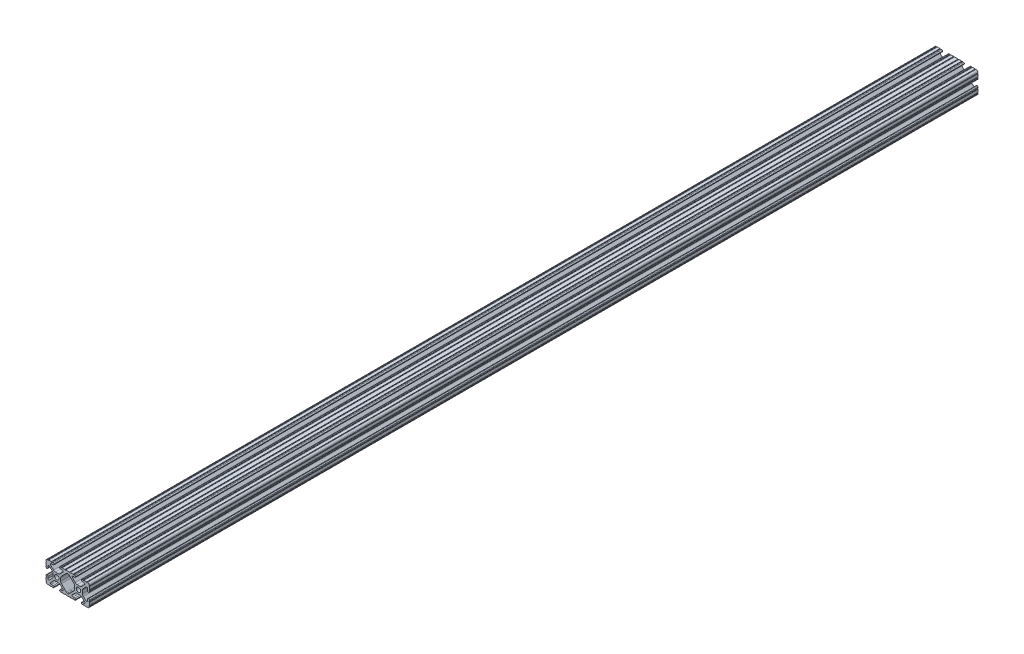
SolidWorks part; units mm, degrees
ref_plane "Front Plane" through (0, 0, 0) normal (0, 0, 1) x (1, 0, 0)
ref_plane "Top Plane" through (0, 0, 0) normal (0, 1, 0) x (1, 0, 0)
ref_plane "Right Plane" through (0, 0, 0) normal (1, 0, 0) x (0, 0, -1)
sketch "Sketch1" plane through (0, 0, 0) normal (0, 0, 1) x (1, 0, 0)
  line L0 (-7.2595, -3.8694) -> (-1.5457, -9.5728)
  line L1 (-8.1915, 1.6223) -> (-8.1915, -1.6223)
  line L2 (-1.504, 9.5765) -> (-7.252, 3.8768)
  line L3 (0.5515, 10.033) -> (-0.3952, 10.033)
  line L4 (7.2829, 3.8459) -> (1.6756, 9.5611)
  line L5 (8.1915, -1.6223) -> (8.1915, 1.6223)
  line L6 (1.5457, -9.5728) -> (7.2595, -3.8694)
  line L7 (-0.4332, -10.033) -> (0.4332, -10.033)
  line L8 (18.0171, 12.7) -> (16.9875, 12.7)
  line L9 (15.9385, 11.651) -> (15.9385, 11.5392)
  line L10 (16.9875, 10.4902) -> (19.1164, 10.4902)
  line L11 (19.8441, 8.7652) -> (16.619, 5.4551)
  line L12 (14.3449, 4.4958) -> (11.0833, 4.4958)
  line L13 (8.817, 5.4472) -> (5.5642, 8.7627)
  line L14 (6.2894, 10.4902) -> (8.4125, 10.4902)
  line L15 (9.4615, 11.5392) -> (9.4615, 11.651)
  line L16 (8.4125, 12.7) -> (7.3829, 12.7)
  line L17 (6.3669, 12.7) -> (3.1496, 12.7)
  line L18 (2.1336, 12.7) -> (-2.1336, 12.7)
  line L19 (-3.1496, 12.7) -> (-6.3669, 12.7)
  line L20 (-7.3829, 12.7) -> (-8.4125, 12.7)
  line L21 (-9.4615, 11.651) -> (-9.4615, 11.5392)
  line L22 (-8.4125, 10.4902) -> (-6.2836, 10.4902)
  line L23 (-5.5326, 8.6661) -> (-8.81, 5.4163)
  line L24 (-11.0455, 4.4958) -> (-14.3545, 4.4958)
  line L25 (-16.59, 5.4163) -> (-19.8674, 8.6661)
  line L26 (-19.1164, 10.4902) -> (-16.9875, 10.4902)
  line L27 (-15.9385, 11.5392) -> (-15.9385, 11.651)
  line L28 (-16.9875, 12.7) -> (-18.0171, 12.7)
  line L29 (-19.0331, 12.7) -> (-22.2504, 12.7)
  line L30 (-25.4, 9.5504) -> (-25.4, 6.3331)
  line L31 (-25.4, 5.3171) -> (-25.4, 4.2375)
  line L32 (-24.401, 3.2385) -> (-24.2392, 3.2385)
  line L33 (-23.1902, 4.2875) -> (-23.1902, 6.3347)
  line L34 (-21.434, 7.0665) -> (-18.148, 3.8082)
  line L35 (-17.2085, 1.5536) -> (-17.2085, -1.6952)
  line L36 (-18.1405, -3.9423) -> (-21.4316, -7.2274)
  line L37 (-23.1902, -6.498) -> (-23.1902, -4.2875)
  line L38 (-24.2392, -3.2385) -> (-24.351, -3.2385)
  line L39 (-25.4, -4.2875) -> (-25.4, -5.3171)
  line L40 (-25.4, -6.3331) -> (-25.4, -9.5504)
  line L41 (-22.2504, -12.7) -> (-19.0331, -12.7)
  line L42 (-18.0171, -12.7) -> (-16.9875, -12.7)
  line L43 (-15.9384, -11.651) -> (-15.9384, -11.5392)
  line L44 (-16.9875, -10.4902) -> (-19.1164, -10.4902)
  line L45 (-19.8341, -8.7551) -> (-16.4966, -5.4237)
  line L46 (-14.2536, -4.4958) -> (-11.1464, -4.4958)
  line L47 (-8.9034, -5.4237) -> (-5.5659, -8.7551)
  line L48 (-6.2836, -10.4902) -> (-8.4125, -10.4902)
  line L49 (-9.4616, -11.5392) -> (-9.4616, -11.651)
  line L50 (-8.4125, -12.7) -> (-7.3829, -12.7)
  line L51 (-6.3669, -12.7) -> (-3.1496, -12.7)
  line L52 (-2.1336, -12.7) -> (2.1336, -12.7)
  line L53 (3.1496, -12.7) -> (6.3669, -12.7)
  line L54 (7.3829, -12.7) -> (8.4125, -12.7)
  line L55 (9.4616, -11.651) -> (9.4616, -11.5392)
  line L56 (8.4125, -10.4902) -> (6.2894, -10.4902)
  line L57 (5.4807, -8.5353) -> (8.5979, -5.4237)
  line L58 (10.8409, -4.4958) -> (14.1026, -4.4958)
  line L59 (16.1879, -5.2766) -> (19.8682, -8.4822)
  line L60 (19.1164, -10.4902) -> (16.9875, -10.4902)
  line L61 (15.9384, -11.5392) -> (15.9384, -11.651)
  line L62 (16.9875, -12.7) -> (18.0171, -12.7)
  line L63 (19.0331, -12.7) -> (22.2504, -12.7)
  line L64 (25.4, -9.5504) -> (25.4, -6.3331)
  line L65 (25.4, -5.3171) -> (25.4, -4.2375)
  line L66 (24.401, -3.2385) -> (24.1892, -3.2385)
  line L67 (23.1902, -4.2375) -> (23.1902, -6.1559)
  line L68 (21.584, -6.8869) -> (18.2982, -4.025)
  line L69 (17.2085, -1.6308) -> (17.2085, 1.6308)
  line L70 (18.1094, 3.8465) -> (21.5263, 7.3534)
  line L71 (23.1902, 6.6769) -> (23.1902, 4.2375)
  line L72 (24.1892, 3.2385) -> (24.401, 3.2385)
  line L73 (25.4, 4.2375) -> (25.4, 5.3171)
  line L74 (25.4, 6.3332) -> (25.4, 9.5504)
  line L75 (22.2504, 12.7) -> (19.0331, 12.7)
  circle A0 centre (-12.7, 0) radius 2.6035
  circle A1 centre (12.7, 0) radius 2.6035
  arc A2 (-1.5457, -9.5728) -> (-0.4332, -10.033) centre (-0.4332, -8.4582) ccw
  arc A3 (-8.1915, -1.6223) -> (-7.2595, -3.8694) centre (-5.0165, -1.6223) ccw
  arc A4 (-7.252, 3.8768) -> (-8.1915, 1.6223) centre (-5.0165, 1.6223) ccw
  arc A5 (-0.3952, 10.033) -> (-1.504, 9.5765) centre (-0.3952, 8.4582) ccw
  arc A6 (1.6756, 9.5611) -> (0.5515, 10.033) centre (0.5515, 8.4582) ccw
  arc A7 (8.1915, 1.6223) -> (7.2829, 3.8459) centre (5.0165, 1.6223) ccw
  arc A8 (7.2595, -3.8694) -> (8.1915, -1.6223) centre (5.0165, -1.6223) ccw
  arc A9 (0.4332, -10.033) -> (1.5457, -9.5728) centre (0.4332, -8.4582) ccw
  arc A10 (18.0171, 12.7) -> (19.0331, 12.7) centre (18.5251, 12.7) ccw
  arc A11 (16.9875, 12.7) -> (15.9385, 11.651) centre (16.9875, 11.651) ccw
  arc A12 (15.9385, 11.5392) -> (16.9875, 10.4902) centre (16.9875, 11.5392) ccw
  arc A13 (19.8441, 8.7652) -> (19.1164, 10.4902) centre (19.1164, 9.4742) ccw
  arc A14 (14.3449, 4.4958) -> (16.619, 5.4551) centre (14.3449, 7.6708) ccw
  arc A15 (8.817, 5.4472) -> (11.0833, 4.4958) centre (11.0833, 7.6708) ccw
  arc A16 (6.2894, 10.4902) -> (5.5642, 8.7627) centre (6.2894, 9.4742) ccw
  arc A17 (8.4125, 10.4902) -> (9.4615, 11.5392) centre (8.4125, 11.5392) ccw
  arc A18 (9.4615, 11.651) -> (8.4125, 12.7) centre (8.4125, 11.651) ccw
  arc A19 (6.3669, 12.7) -> (7.3829, 12.7) centre (6.8749, 12.7) ccw
  arc A20 (2.1336, 12.7) -> (3.1496, 12.7) centre (2.6416, 12.7) ccw
  arc A21 (-3.1496, 12.7) -> (-2.1336, 12.7) centre (-2.6416, 12.7) ccw
  arc A22 (-7.3829, 12.7) -> (-6.3669, 12.7) centre (-6.8749, 12.7) ccw
  arc A23 (-8.4125, 12.7) -> (-9.4615, 11.651) centre (-8.4125, 11.651) ccw
  arc A24 (-9.4615, 11.5392) -> (-8.4125, 10.4902) centre (-8.4125, 11.5392) ccw
  arc A25 (-5.5326, 8.6661) -> (-6.2836, 10.4902) centre (-6.2836, 9.4235) ccw
  arc A26 (-11.0455, 4.4958) -> (-8.81, 5.4163) centre (-11.0455, 7.6708) ccw
  arc A27 (-16.59, 5.4163) -> (-14.3545, 4.4958) centre (-14.3545, 7.6708) ccw
  arc A28 (-19.1164, 10.4902) -> (-19.8674, 8.6661) centre (-19.1164, 9.4235) ccw
  arc A29 (-16.9875, 10.4902) -> (-15.9385, 11.5392) centre (-16.9875, 11.5392) ccw
  arc A30 (-15.9385, 11.651) -> (-16.9875, 12.7) centre (-16.9875, 11.651) ccw
  arc A31 (-19.0331, 12.7) -> (-18.0171, 12.7) centre (-18.5251, 12.7) ccw
  arc A32 (-23.2664, 12.6998) -> (-22.2504, 12.7) centre (-22.7584, 12.7) ccw
  arc A33 (-23.2664, 12.6998) -> (-25.3998, 10.5664) centre (-23.2918, 10.5918) ccw
  arc A34 (-25.4, 9.5504) -> (-25.3998, 10.5664) centre (-25.4, 10.0584) ccw
  arc A35 (-25.4, 5.3171) -> (-25.4, 6.3331) centre (-25.4, 5.8251) ccw
  arc A36 (-25.4, 4.2375) -> (-24.401, 3.2385) centre (-24.401, 4.2375) ccw
  arc A37 (-24.2392, 3.2385) -> (-23.1902, 4.2875) centre (-24.2392, 4.2875) ccw
  arc A38 (-21.434, 7.0665) -> (-23.1902, 6.3347) centre (-22.1596, 6.3347) ccw
  arc A39 (-17.2085, 1.5536) -> (-18.148, 3.8082) centre (-20.3835, 1.5536) ccw
  arc A40 (-18.1405, -3.9423) -> (-17.2085, -1.6952) centre (-20.3835, -1.6952) ccw
  arc A41 (-23.1902, -6.498) -> (-21.4316, -7.2274) centre (-22.1596, -6.498) ccw
  arc A42 (-23.1902, -4.2875) -> (-24.2392, -3.2385) centre (-24.2392, -4.2875) ccw
  arc A43 (-24.351, -3.2385) -> (-25.4, -4.2875) centre (-24.351, -4.2875) ccw
  arc A44 (-25.4, -6.3331) -> (-25.4, -5.3171) centre (-25.4, -5.8251) ccw
  arc A45 (-25.3998, -10.5664) -> (-25.4, -9.5504) centre (-25.4, -10.0584) ccw
  arc A46 (-25.3998, -10.5664) -> (-23.2664, -12.6998) centre (-23.2918, -10.5918) ccw
  arc A47 (-22.2504, -12.7) -> (-23.2664, -12.6998) centre (-22.7584, -12.7) ccw
  arc A48 (-18.0171, -12.7) -> (-19.0331, -12.7) centre (-18.5251, -12.7) ccw
  arc A49 (-16.9875, -12.7) -> (-15.9384, -11.651) centre (-16.9875, -11.651) ccw
  arc A50 (-15.9384, -11.5392) -> (-16.9875, -10.4902) centre (-16.9875, -11.5392) ccw
  arc A51 (-19.8341, -8.7551) -> (-19.1164, -10.4902) centre (-19.1164, -9.4742) ccw
  arc A52 (-14.2536, -4.4958) -> (-16.4966, -5.4237) centre (-14.2536, -7.6708) ccw
  arc A53 (-8.9034, -5.4237) -> (-11.1464, -4.4958) centre (-11.1464, -7.6708) ccw
  arc A54 (-6.2836, -10.4902) -> (-5.5659, -8.7551) centre (-6.2836, -9.4742) ccw
  arc A55 (-8.4125, -10.4902) -> (-9.4616, -11.5392) centre (-8.4125, -11.5392) ccw
  arc A56 (-9.4616, -11.651) -> (-8.4125, -12.7) centre (-8.4125, -11.651) ccw
  arc A57 (-6.3669, -12.7) -> (-7.3829, -12.7) centre (-6.8749, -12.7) ccw
  arc A58 (-2.1336, -12.7) -> (-3.1496, -12.7) centre (-2.6416, -12.7) ccw
  arc A59 (3.1496, -12.7) -> (2.1336, -12.7) centre (2.6416, -12.7) ccw
  arc A60 (7.3829, -12.7) -> (6.3669, -12.7) centre (6.8749, -12.7) ccw
  arc A61 (8.4125, -12.7) -> (9.4616, -11.651) centre (8.4125, -11.651) ccw
  arc A62 (9.4616, -11.5392) -> (8.4125, -10.4902) centre (8.4125, -11.5392) ccw
  arc A63 (5.4807, -8.5353) -> (6.2894, -10.4902) centre (6.2894, -9.3455) ccw
  arc A64 (10.8409, -4.4958) -> (8.5979, -5.4237) centre (10.8409, -7.6708) ccw
  arc A65 (16.1879, -5.2766) -> (14.1026, -4.4958) centre (14.1026, -7.6708) ccw
  arc A66 (19.1164, -10.4902) -> (19.8682, -8.4822) centre (19.1164, -9.3455) ccw
  arc A67 (16.9875, -10.4902) -> (15.9384, -11.5392) centre (16.9875, -11.5392) ccw
  arc A68 (15.9384, -11.651) -> (16.9875, -12.7) centre (16.9875, -11.651) ccw
  arc A69 (19.0331, -12.7) -> (18.0171, -12.7) centre (18.5251, -12.7) ccw
  arc A70 (23.2664, -12.6998) -> (22.2504, -12.7) centre (22.7584, -12.7) ccw
  arc A71 (23.2664, -12.6998) -> (25.3998, -10.5664) centre (23.2918, -10.5918) ccw
  arc A72 (25.4, -9.5504) -> (25.3998, -10.5664) centre (25.4, -10.0584) ccw
  arc A73 (25.4, -5.3171) -> (25.4, -6.3331) centre (25.4, -5.8251) ccw
  arc A74 (25.4, -4.2375) -> (24.401, -3.2385) centre (24.401, -4.2375) ccw
  arc A75 (24.1892, -3.2385) -> (23.1902, -4.2375) centre (24.1892, -4.2375) ccw
  arc A76 (21.584, -6.8869) -> (23.1902, -6.1559) centre (22.2207, -6.1559) ccw
  arc A77 (17.2085, -1.6308) -> (18.2982, -4.025) centre (20.3835, -1.6308) ccw
  arc A78 (18.1094, 3.8465) -> (17.2085, 1.6308) centre (20.3835, 1.6308) ccw
  arc A79 (23.1902, 6.6769) -> (21.5263, 7.3534) centre (22.2207, 6.6769) ccw
  arc A80 (23.1902, 4.2375) -> (24.1892, 3.2385) centre (24.1892, 4.2375) ccw
  arc A81 (24.401, 3.2385) -> (25.4, 4.2375) centre (24.401, 4.2375) ccw
  arc A82 (25.4, 6.3332) -> (25.4, 5.3171) centre (25.4, 5.8251) ccw
  arc A83 (25.3998, 10.5664) -> (25.4, 9.5504) centre (25.4, 10.0584) ccw
  arc A84 (25.3998, 10.5664) -> (23.2664, 12.6998) centre (23.2918, 10.5918) ccw
  arc A85 (22.2504, 12.7) -> (23.2664, 12.6998) centre (22.7584, 12.7) ccw
  point P248 (0, 10.033)
extrude "Boss-Extrude1" add sketch "Sketch1" along normal mid plane 1041.4
sketch "Sketch2" plane through (17.2085, 0, 0) normal (1, 0, 0) x (0, 0, -1)
  line L0 (520.7, -1.6308) -> (520.7, 1.6308) construction
  line L1 (0, 0) -> (0, 82.9932) construction
  circle A0 centre (508, 0) radius 3.175
  circle A1 centre (-508, 0) radius 3.175
  dimension "D1" = 6.35
  dimension "D2" = 12.7
extrude "Cut-Extrude1" cut sketch "Sketch2" against normal through all both and the other way through all
